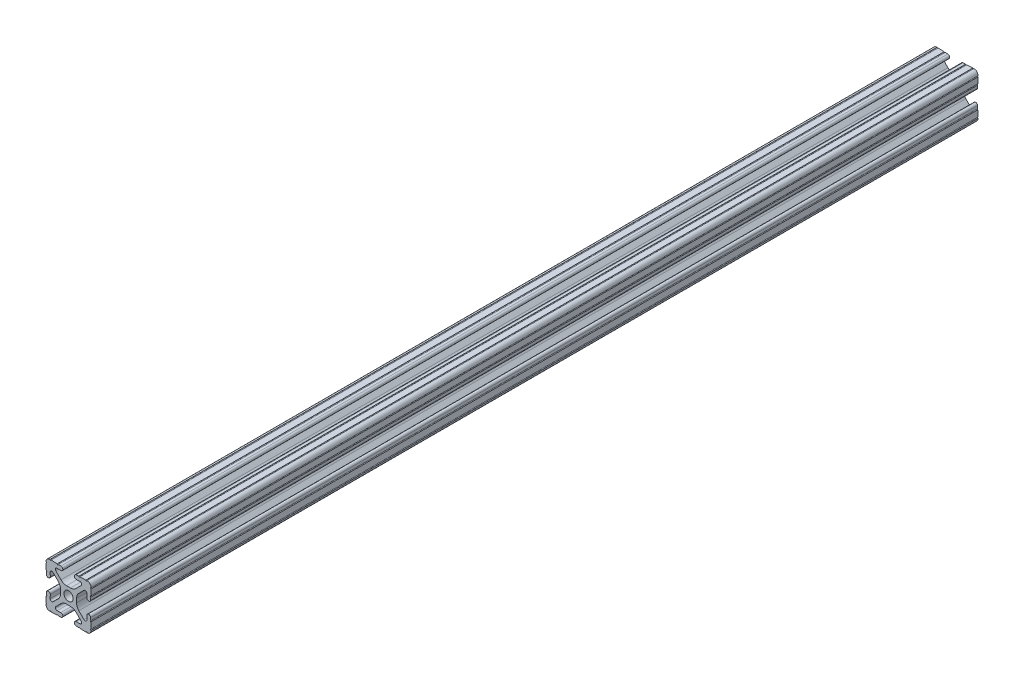
SolidWorks part; units mm, degrees
material "6063-T5"
ref_plane "Front Plane" through (0, 0, 0) normal (0, 0, 1) x (1, 0, 0)
ref_plane "Top Plane" through (0, 0, 0) normal (0, 1, 0) x (1, 0, 0)
ref_plane "Right Plane" through (0, 0, 0) normal (1, 0, 0) x (0, 0, -1)
sketch "Sketch1" plane through (0, 0, 0) normal (0, 0, 1) x (1, 0, 0)
  line L0 (0, 12.7) -> (-12.7814, 12.7) construction
  line L1 (-4.5085, 0) -> (-4.5085, 2.9459)
  line L2 (-6.0437, 12.5461) -> (-10.0976, 12.6876) construction
  line L3 (-11.5616, 12.4229) -> (-4.3159, 12.1699) construction
  line L4 (-6.4364, 10.3486) -> (-6.3592, 12.5571) construction
  line L6 (-2.9459, 4.5085) -> (0, 4.5085)
  line L7 (0, 0) -> (0, 12.7) construction
  line L8 (0, 0) -> (-12.7814, 0) construction
  line L9 (0.7813, 0.7813) -> (-0.7813, -0.7813) construction
  line L10 (-2.9459, 4.5085) -> (-7.1484, 8.711)
  line L11 (-4.5085, 2.9459) -> (-8.711, 7.1484)
  line L13 (0, 0) -> (-12.7814, 12.7814) construction
  line L14 (-10.4131, 12.6987) -> (-4.3048, 12.4853)
  line L15 (-4.3048, 12.4853) -> (-4.382, 10.2769) construction
  line L16 (-4.382, 10.2769) -> (-6.4364, 10.3486)
  line L17 (-12.6987, 10.4131) -> (-12.4853, 4.3048)
  line L18 (-10.2769, 4.382) -> (-10.3486, 6.4364)
  circle A0 centre (0, 0) radius 2.6035
  arc A1 (-4.382, 10.2769) -> (-4.3048, 12.4853) centre (-4.3434, 11.3811) ccw
  arc A2 (-7.1484, 8.711) -> (-6.4364, 10.3486) centre (-6.4698, 9.3896) cw
  arc A3 (-8.711, 7.1484) -> (-10.3486, 6.4364) centre (-9.3896, 6.4698) ccw
  arc A4 (-10.2769, 4.382) -> (-12.4853, 4.3048) centre (-11.3811, 4.3434) cw
  arc A5 (-10.4131, 12.6987) -> (-12.6987, 10.4131) centre (-10.4902, 10.4902) ccw
  arc A6 (-10.4131, 12.6987) -> (-9.7821, 12.6766) centre (-10.0976, 12.6876) ccw
  arc A7 (-6.3592, 12.5571) -> (-5.7282, 12.5351) centre (-6.0437, 12.5461) ccw
  arc A8 (-12.5571, 6.3592) -> (-12.5351, 5.7282) centre (-12.5461, 6.0437) cw
  arc A9 (-12.6987, 10.4131) -> (-12.6766, 9.7821) centre (-12.6876, 10.0976) cw
  dimension "D1" = 5.207
  dimension "D5" = 14.859
  dimension "D9" = 2
  dimension "D2" = 25.4
  dimension "D12" = 0.6314
  dimension "D10" = 2.2098
  dimension "D3" = 9.017
  dimension "D4" = 9.017
  dimension "D6" = 25.4
  dimension "D7" = 6.477
  dimension "D8" = 2.2098
  dimension "D11" = 12.7
sketch "Sketch3" plane through (0, 0, 0) normal (0, 0, 1) x (1, 0, 0)
  line L0 (-2.9459, 4.5085) -> (0, 4.5085) construction
  line L1 (-2.9459, 4.5085) -> (-7.1484, 8.711) construction
  line L2 (-4.382, 10.2769) -> (-6.4364, 10.3486) construction
  line L3 (-10.4131, 12.6987) -> (-4.3048, 12.4853) construction
  line L4 (-4.5085, 0) -> (-4.5085, 2.9459) construction
  line L5 (-4.5085, 2.9459) -> (-8.711, 7.1484) construction
  line L6 (-10.2769, 4.382) -> (-10.3486, 6.4364) construction
  line L7 (-12.6987, 10.4131) -> (-12.4853, 4.3048) construction
  line L8 (-1.1153, 4.5085) -> (1.1153, 4.5085)
  line L9 (-4.2404, 5.803) -> (-7.1484, 8.711)
  line L10 (-4.382, 10.2769) -> (-6.4364, 10.3486)
  line L11 (-9.7821, 12.6766) -> (-6.3592, 12.5571)
  line L12 (-4.5085, -1.1153) -> (-4.5085, 1.1153)
  line L13 (-5.803, 4.2404) -> (-8.711, 7.1484)
  line L14 (-10.2769, 4.382) -> (-10.3486, 6.4364)
  line L15 (-12.6766, 9.7821) -> (-12.5571, 6.3592)
  line L16 (-5.7282, 12.5351) -> (-4.3048, 12.4853)
  line L17 (-12.5351, 5.7282) -> (-12.4853, 4.3048)
  line L18 (0, 0) -> (0, 12.7) construction
  line L19 (0, 0) -> (-12.7814, 0) construction
  line L20 (12.5351, 5.7282) -> (12.4853, 4.3048)
  line L21 (5.7282, 12.5351) -> (4.3048, 12.4853)
  line L22 (12.6766, 9.7821) -> (12.5571, 6.3592)
  line L23 (10.2769, 4.382) -> (10.3486, 6.4364)
  line L24 (5.803, 4.2404) -> (8.711, 7.1484)
  line L25 (4.5085, -1.1153) -> (4.5085, 1.1153)
  line L26 (9.7821, 12.6766) -> (6.3592, 12.5571)
  line L27 (4.382, 10.2769) -> (6.4364, 10.3486)
  line L28 (4.2404, 5.803) -> (7.1484, 8.711)
  line L29 (4.2404, -5.803) -> (7.1484, -8.711)
  line L30 (4.382, -10.2769) -> (6.4364, -10.3486)
  line L31 (9.7821, -12.6766) -> (6.3592, -12.5571)
  line L32 (5.803, -4.2404) -> (8.711, -7.1484)
  line L33 (10.2769, -4.382) -> (10.3486, -6.4364)
  line L34 (12.6766, -9.7821) -> (12.5571, -6.3592)
  line L35 (5.7282, -12.5351) -> (4.3048, -12.4853)
  line L36 (12.5351, -5.7282) -> (12.4853, -4.3048)
  line L37 (-12.5351, -5.7282) -> (-12.4853, -4.3048)
  line L38 (-5.7282, -12.5351) -> (-4.3048, -12.4853)
  line L39 (-12.6766, -9.7821) -> (-12.5571, -6.3592)
  line L40 (-10.2769, -4.382) -> (-10.3486, -6.4364)
  line L41 (-5.803, -4.2404) -> (-8.711, -7.1484)
  line L42 (-9.7821, -12.6766) -> (-6.3592, -12.5571)
  line L43 (-4.382, -10.2769) -> (-6.4364, -10.3486)
  line L44 (-4.2404, -5.803) -> (-7.1484, -8.711)
  line L45 (-1.1153, -4.5085) -> (1.1153, -4.5085)
  arc A0 (-10.4131, 12.6987) -> (-9.7821, 12.6766) centre (-10.0976, 12.6876) ccw construction
  arc A1 (-6.4364, 10.3486) -> (-7.1484, 8.711) centre (-6.4698, 9.3896) ccw construction
  arc A2 (-4.382, 10.2769) -> (-4.3048, 12.4853) centre (-4.3434, 11.3811) ccw construction
  arc A3 (-8.711, 7.1484) -> (-10.3486, 6.4364) centre (-9.3896, 6.4698) ccw construction
  arc A4 (-12.4853, 4.3048) -> (-10.2769, 4.382) centre (-11.3811, 4.3434) ccw construction
  arc A5 (-6.3592, 12.5571) -> (-5.7282, 12.5351) centre (-6.0437, 12.5461) ccw construction
  arc A6 (-10.4131, 12.6987) -> (-12.6987, 10.4131) centre (-10.4902, 10.4902) ccw construction
  arc A7 (-12.6766, 9.7821) -> (-12.6987, 10.4131) centre (-12.6876, 10.0976) ccw construction
  arc A8 (-12.5351, 5.7282) -> (-12.5571, 6.3592) centre (-12.5461, 6.0437) ccw construction
  arc A9 (-10.4131, 12.6987) -> (-9.7821, 12.6766) centre (-10.0976, 12.6876) ccw
  arc A10 (-6.4364, 10.3486) -> (-7.1484, 8.711) centre (-6.4698, 9.3896) ccw
  arc A11 (-4.382, 10.2769) -> (-4.3048, 12.4853) centre (-4.3434, 11.3811) ccw
  arc A12 (-8.711, 7.1484) -> (-10.3486, 6.4364) centre (-9.3896, 6.4698) ccw
  arc A13 (-12.4853, 4.3048) -> (-10.2769, 4.382) centre (-11.3811, 4.3434) ccw
  arc A14 (-6.3592, 12.5571) -> (-5.7282, 12.5351) centre (-6.0437, 12.5461) ccw
  arc A15 (-10.4131, 12.6987) -> (-12.6987, 10.4131) centre (-10.4902, 10.4902) ccw
  arc A16 (-12.6766, 9.7821) -> (-12.6987, 10.4131) centre (-12.6876, 10.0976) ccw
  arc A17 (-12.5351, 5.7282) -> (-12.5571, 6.3592) centre (-12.5461, 6.0437) ccw
  arc A18 (-1.1153, 4.5085) -> (-4.2404, 5.803) centre (-1.1153, 8.9281) cw
  arc A19 (4.5085, 1.1153) -> (5.803, 4.2404) centre (8.9281, 1.1153) cw
  arc A20 (1.1153, 4.5085) -> (4.2404, 5.803) centre (1.1153, 8.9281) ccw
  arc A21 (-4.5085, 1.1153) -> (-5.803, 4.2404) centre (-8.9281, 1.1153) ccw
  arc A22 (12.5351, 5.7282) -> (12.5571, 6.3592) centre (12.5461, 6.0437) cw
  arc A23 (12.6766, 9.7821) -> (12.6987, 10.4131) centre (12.6876, 10.0976) cw
  arc A24 (10.4131, 12.6987) -> (12.6987, 10.4131) centre (10.4902, 10.4902) cw
  arc A25 (6.3592, 12.5571) -> (5.7282, 12.5351) centre (6.0437, 12.5461) cw
  arc A26 (12.4853, 4.3048) -> (10.2769, 4.382) centre (11.3811, 4.3434) cw
  arc A27 (8.711, 7.1484) -> (10.3486, 6.4364) centre (9.3896, 6.4698) cw
  arc A28 (4.382, 10.2769) -> (4.3048, 12.4853) centre (4.3434, 11.3811) cw
  arc A29 (6.4364, 10.3486) -> (7.1484, 8.711) centre (6.4698, 9.3896) cw
  arc A30 (10.4131, 12.6987) -> (9.7821, 12.6766) centre (10.0976, 12.6876) cw
  arc A31 (10.4131, -12.6987) -> (9.7821, -12.6766) centre (10.0976, -12.6876) ccw
  arc A32 (6.4364, -10.3486) -> (7.1484, -8.711) centre (6.4698, -9.3896) ccw
  arc A33 (4.382, -10.2769) -> (4.3048, -12.4853) centre (4.3434, -11.3811) ccw
  arc A34 (8.711, -7.1484) -> (10.3486, -6.4364) centre (9.3896, -6.4698) ccw
  arc A35 (12.4853, -4.3048) -> (10.2769, -4.382) centre (11.3811, -4.3434) ccw
  arc A36 (6.3592, -12.5571) -> (5.7282, -12.5351) centre (6.0437, -12.5461) ccw
  arc A37 (10.4131, -12.6987) -> (12.6987, -10.4131) centre (10.4902, -10.4902) ccw
  arc A38 (12.6766, -9.7821) -> (12.6987, -10.4131) centre (12.6876, -10.0976) ccw
  arc A39 (12.5351, -5.7282) -> (12.5571, -6.3592) centre (12.5461, -6.0437) ccw
  arc A40 (-4.5085, -1.1153) -> (-5.803, -4.2404) centre (-8.9281, -1.1153) cw
  arc A41 (1.1153, -4.5085) -> (4.2404, -5.803) centre (1.1153, -8.9281) cw
  arc A42 (4.5085, -1.1153) -> (5.803, -4.2404) centre (8.9281, -1.1153) ccw
  arc A43 (-1.1153, -4.5085) -> (-4.2404, -5.803) centre (-1.1153, -8.9281) ccw
  arc A44 (-12.5351, -5.7282) -> (-12.5571, -6.3592) centre (-12.5461, -6.0437) cw
  arc A45 (-12.6766, -9.7821) -> (-12.6987, -10.4131) centre (-12.6876, -10.0976) cw
  arc A46 (-10.4131, -12.6987) -> (-12.6987, -10.4131) centre (-10.4902, -10.4902) cw
  arc A47 (-6.3592, -12.5571) -> (-5.7282, -12.5351) centre (-6.0437, -12.5461) cw
  arc A48 (-12.4853, -4.3048) -> (-10.2769, -4.382) centre (-11.3811, -4.3434) cw
  arc A49 (-8.711, -7.1484) -> (-10.3486, -6.4364) centre (-9.3896, -6.4698) cw
  arc A50 (-4.382, -10.2769) -> (-4.3048, -12.4853) centre (-4.3434, -11.3811) cw
  arc A51 (-6.4364, -10.3486) -> (-7.1484, -8.711) centre (-6.4698, -9.3896) cw
  arc A52 (-10.4131, -12.6987) -> (-9.7821, -12.6766) centre (-10.0976, -12.6876) cw
  circle A53 centre (0, 0) radius 2.6035 construction
  circle A54 centre (0, 0) radius 2.6035
  point P135 (4.5085, 0)
  dimension "D2" = 4.4196
extrude "Extrude1" add sketch "Sketch3" along normal mid plane 1219.2
sketch "Sketch5" plane through (0.4302, 12.32, 0) normal (0.0349, 0.9994, 0) x (0.9994, -0.0349, 0)
  line L1 (-39.0506, 609.6) -> (26.8771, 609.6)
  line L2 (-39.0506, 609.6) -> (-39.0506, -109.6)
  line L3 (-39.0506, -109.6) -> (26.8771, -109.6)
  line L4 (26.8771, 609.6) -> (26.8771, -109.6)
  dimension "D1" = 0
  dimension "D2" = 719.2
extrude "Cut-Extrude1" cut sketch "Sketch5" against normal blind 34 and the other way blind 10
equation "\"D10@Sketch1\" = \"D8@Sketch1\""
equation "\"D11@Sketch1\" = \"D6@Sketch1\"/2"
equation "\"D12@Sketch1\" = \"D8@Sketch1\"/3.5"
equation "\"D2@Sketch3\" = \"D8@Sketch1\"*2"
